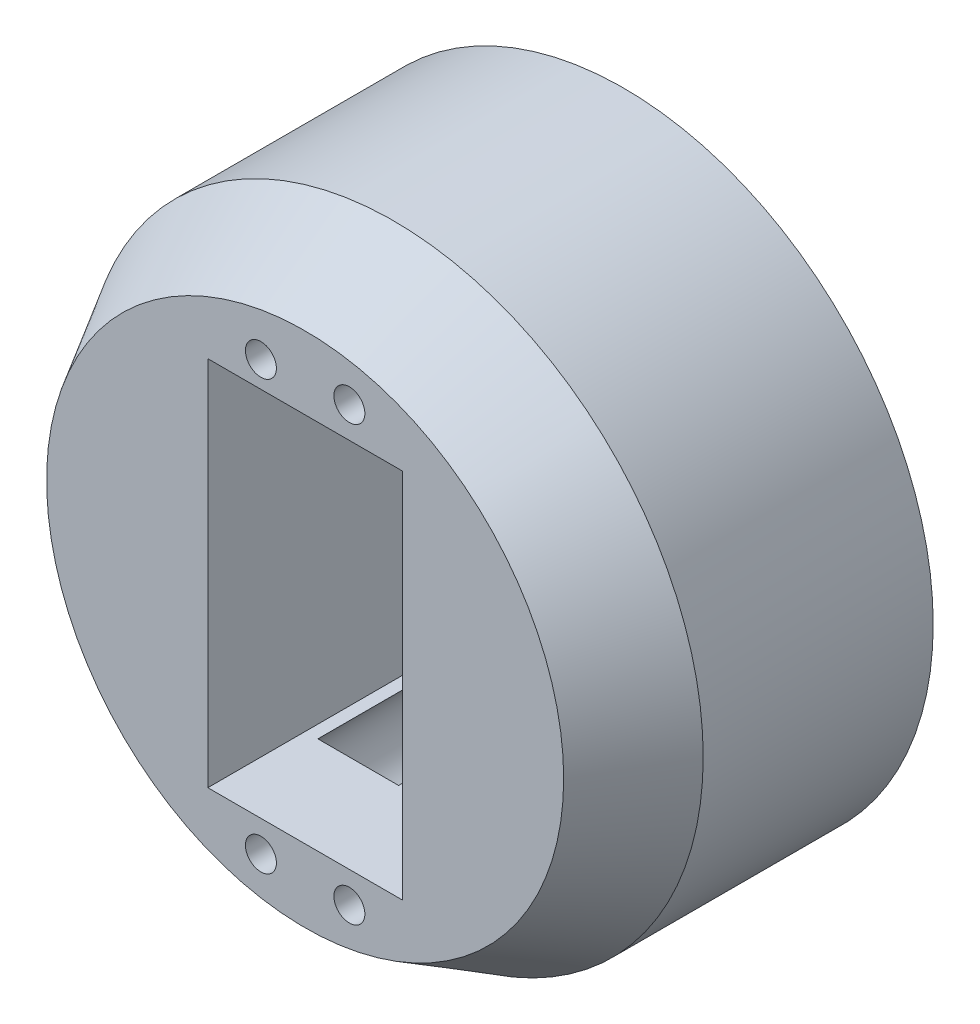
SolidWorks part; units mm, degrees
ref_plane "Front Plane" through (0, 0, 0) normal (0, 0, 1) x (1, 0, 0)
ref_plane "Top Plane" through (0, 0, 0) normal (0, 1, 0) x (1, 0, 0)
ref_plane "Right Plane" through (0, 0, 0) normal (1, 0, 0) x (0, 0, -1)
sketch "Sketch1" plane through (0, 0, 0) normal (0, 0, 1) x (1, 0, 0)
  circle A0 centre (0, 0) radius 35
  dimension "D1" = 70
extrude "Boss-Extrude1" add sketch "Sketch1" along normal blind 36
chamfer "Chamfer1" distance 10 angle 30 1 edges at (35, 0, 36)
sketch "Sketch2" plane through (0, 0, 36) normal (0, 0, 1) x (1, 0, 0)
  line L1 (-11, -21) -> (11, -21)
  line L2 (-11, -21) -> (-11, 21)
  line L3 (-11, 21) -> (11, 21)
  line L4 (11, -21) -> (11, 21)
  line L5 (-11, -21) -> (11, 21) construction
  line L6 (-11, 21) -> (11, -21) construction
  point P0 (0, 0)
  dimension "D1" = 22
  dimension "D2" = 42
extrude "Cut-Extrude1" cut sketch "Sketch2" against normal through all
sketch "Sketch3" plane through (0, 0, 36) normal (0, 0, 1) x (1, 0, 0)
  line L1 (-5, 24.5) -> (5, 24.5) construction
  line L2 (-5, 24.5) -> (-5, -24.5) construction
  line L3 (-5, -24.5) -> (5, -24.5) construction
  line L4 (5, 24.5) -> (5, -24.5) construction
  line L5 (-5, 24.5) -> (5, -24.5) construction
  line L6 (-5, -24.5) -> (5, 24.5) construction
  circle A0 centre (-5, 23.9271) radius 1.75
  circle A1 centre (5, 24.5) radius 1.75
  circle A2 centre (5, -24.5) radius 1.75
  circle A3 centre (-5, -24.5) radius 1.75
  point P0 (0, 0)
  dimension "D2" = 3.5
  dimension "D1" = 49
  dimension "10" = 10
extrude "Cut-Extrude2" cut sketch "Sketch3" against normal through all
sketch "Sketch4" plane through (0, 0, 0) normal (0, 0, -1) x (-1, 0, 0)
  circle A0 centre (-5, -24.5) radius 1.75 construction
  circle A1 centre (5, -24.5) radius 1.75 construction
  circle A2 centre (5, 23.9271) radius 1.75 construction
  circle A3 centre (-5, 24.5) radius 1.75 construction
  circle A4 centre (-5, -24.5) radius 1.75
  circle A5 centre (5, -24.5) radius 1.75
  circle A6 centre (5, 23.9271) radius 1.75
  circle A7 centre (-5, 24.5) radius 1.75
  arc A8 (0, -21.6605) -> (0, -27.3395) centre (-5, -24.5) ccw
  arc A9 (0, -27.3395) -> (0, -21.6605) centre (5, -24.5) ccw
  arc A10 (-0.1616, 21.3932) -> (0.1616, 27.0339) centre (5, 23.9271) ccw
  arc A11 (0.1616, 27.0339) -> (-0.1616, 21.3932) centre (-5, 24.5) ccw
  circle A12 centre (5, 23.9271) radius 5.75 construction
  circle A13 centre (-5, 24.5) radius 5.75 construction
  circle A14 centre (5, -24.5) radius 5.75 construction
  circle A15 centre (-5, -24.5) radius 5.75 construction
  dimension "D1" = 4
extrude "Cut-Extrude3" cut sketch "Sketch4" against normal blind 25
